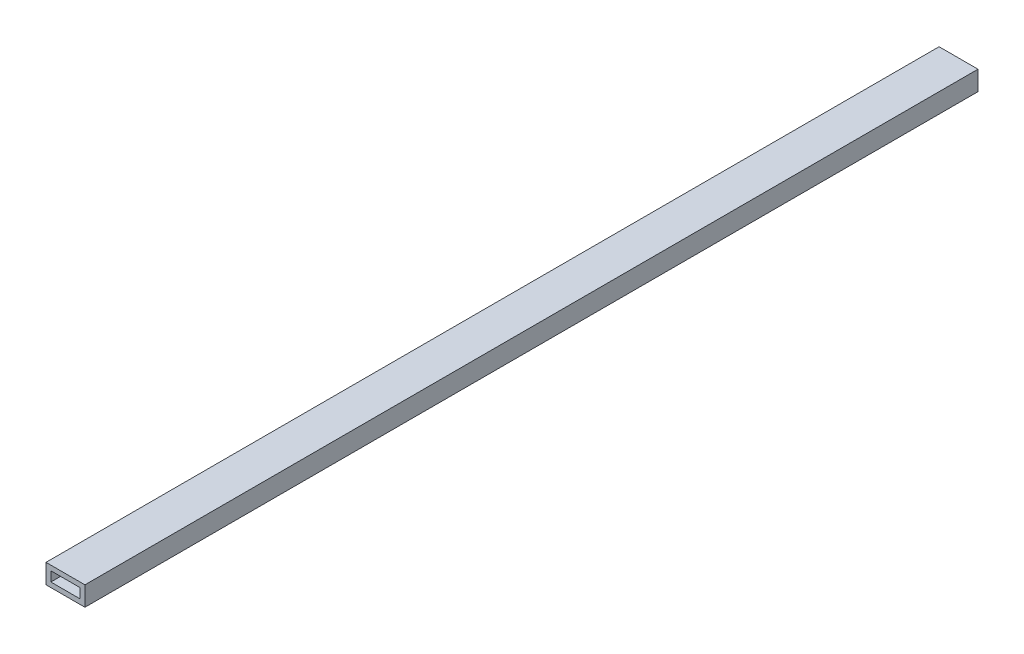
SolidWorks part; units mm, degrees
ref_plane "Front" through (0, 0, 0) normal (0, 0, 1) x (1, 0, 0)
ref_plane "Top" through (0, 0, 0) normal (0, 1, 0) x (1, 0, 0)
ref_plane "Right" through (0, 0, 0) normal (1, 0, 0) x (0, 0, -1)
sketch "Sketch1" plane through (0, 0, 0) normal (0, 0, 1) x (1, 0, 0)
  line L1 (-25.2842, 14.9139) -> (0.1158, 14.9139)
  line L2 (-25.2842, 14.9139) -> (-25.2842, 2.2139)
  line L3 (-25.2842, 2.2139) -> (0.1158, 2.2139)
  line L4 (0.1158, 14.9139) -> (0.1158, 2.2139)
  dimension "D1" = 25.4
  dimension "D2" = 12.7
extrude "Boss-Extrude1" add sketch "Sketch1" along normal blind 582.676
sketch "Sketch2" plane through (0, 0, 0) normal (0, 0, -1) x (-1, 0, 0)
  line L8 (22.1092, 5.3889) -> (22.1092, 11.7389)
  line L9 (22.1092, 11.7389) -> (3.0592, 11.7389)
  line L10 (3.0592, 11.7389) -> (3.0592, 5.3889)
  line L11 (3.0592, 5.3889) -> (22.1092, 5.3889)
  line L12 (22.1092, 5.3889) -> (22.1092, 11.7389)
  line L13 (22.1092, 11.7389) -> (3.0592, 11.7389)
  line L14 (3.0592, 11.7389) -> (3.0592, 5.3889)
  line L15 (3.0592, 5.3889) -> (22.1092, 5.3889)
  dimension "D1" = 3.175
extrude "Cut-Extrude1" cut sketch "Sketch2" against normal through all
